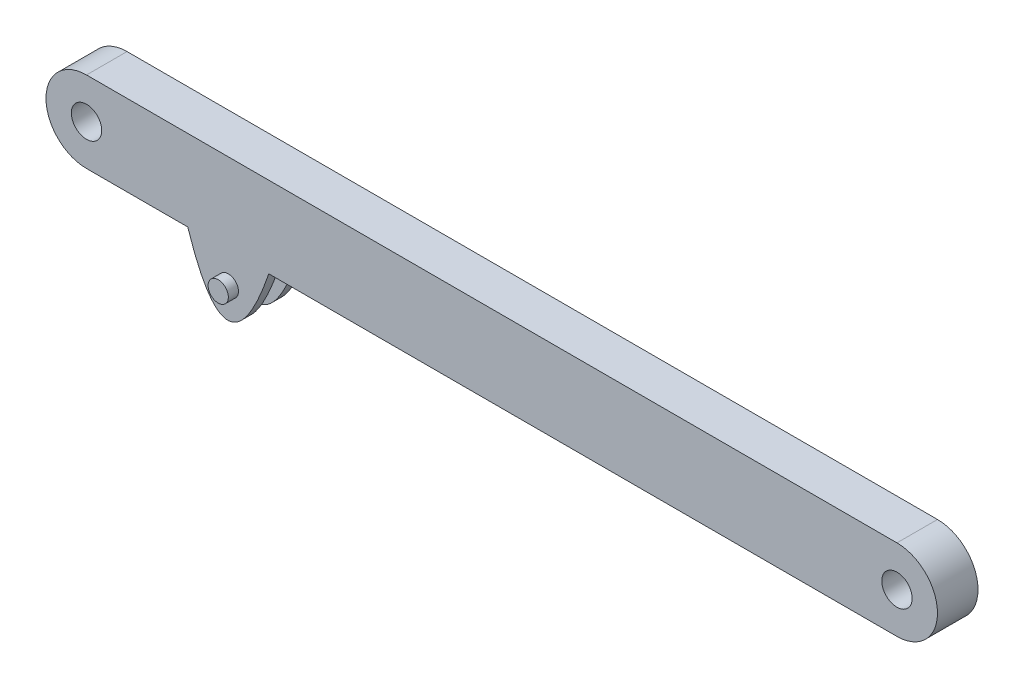
SolidWorks part; units mm, degrees
material "AISI 304"
ref_plane "Front Plane" through (0, 0, 0) normal (0, 0, 1) x (1, 0, 0)
ref_plane "Top Plane" through (0, 0, 0) normal (0, 1, 0) x (1, 0, 0)
ref_plane "Right Plane" through (0, 0, 0) normal (1, 0, 0) x (0, 0, -1)
sketch "Sketch2" plane through (0, 0, 0) normal (0, 0, 1) x (1, 0, 0)
  line L0 (-200, 0) -> (200, 0) construction
  line L1 (-200, 20) -> (200, 20)
  line L2 (-200, -20) -> (200, -20)
  arc A0 (-200, 20) -> (-200, -20) centre (-200, 0) ccw
  arc A1 (200, -20) -> (200, 20) centre (200, 0) ccw
  point P2 (0, 0)
extrude "Boss-Extrude1" add sketch "Sketch2" along normal blind 20
sketch "Sketch4" plane through (0, 0, 20) normal (0, 0, 1) x (1, 0, 0)
  circle A0 centre (-200, 0) radius 7.5
  circle A1 centre (200, 0) radius 7.5
extrude "Cut-Extrude1" cut sketch "Sketch4" against normal blind 20 contours A1 | A0
ref_plane "Plane1" through (0, 0, 10) normal (0, 0, 1) x (1, 0, 0)
sketch "Sketch8" plane through (0, 0, 0) normal (0, 0, 1) x (1, 0, 0)
  line L0 (-150.0376, -20) -> (-110.0376, -20)
  line L1 (-200, -20) -> (200, -20) construction
  spline S0 degree 2 poles (-150.0376, -20) (-130.4932, -80.0015) (-110.0376, -20) knots 0 0 0 1 1 1
extrude "Boss-Extrude2" add sketch "Sketch8" along normal blind 5
sketch "Sketch9" plane through (0, 0, 0) normal (0, 0, 1) x (1, 0, 0)
  circle A0 centre (-130, -35) radius 5
extrude "Boss-Extrude3" add sketch "Sketch9" along normal blind 10 and the other way blind 5
mirror "Mirror2" about plane through (0, 0, 10) normal (0, 0, 1) of "Boss-Extrude3", "Boss-Extrude2"
